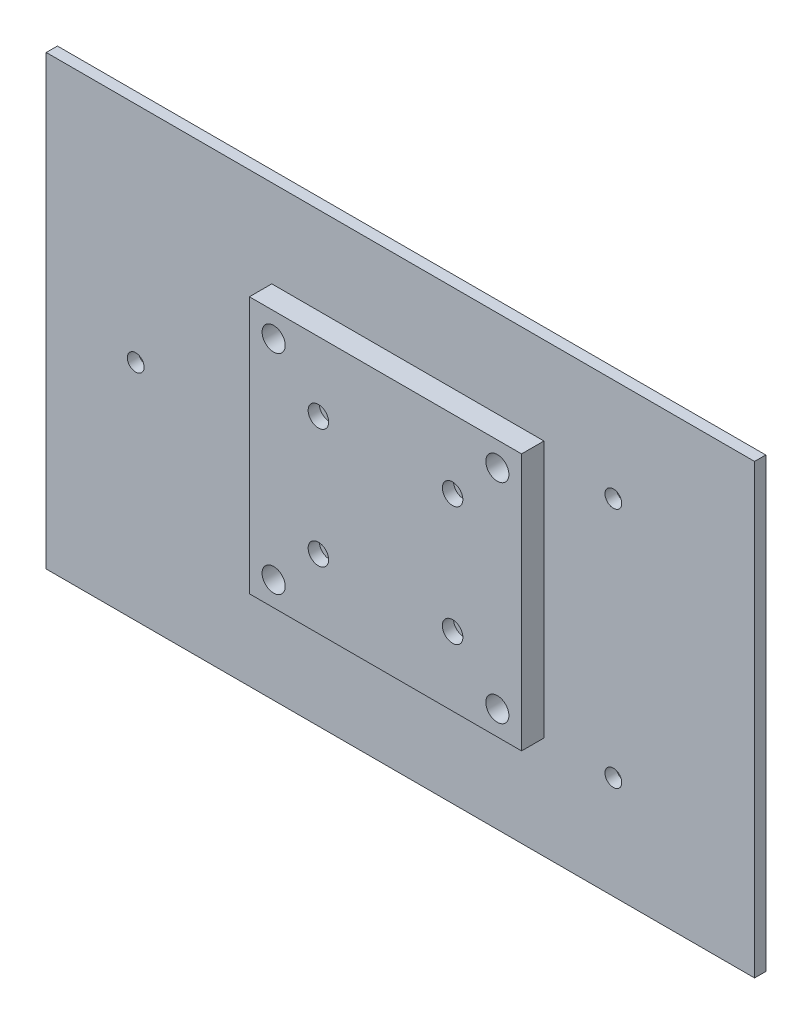
SolidWorks part; units mm, degrees
ref_plane "Alzado" through (0, 0, 0) normal (0, 0, 1) x (1, 0, 0)
ref_plane "Planta" through (0, 0, 0) normal (0, 1, 0) x (1, 0, 0)
ref_plane "Vista lateral" through (0, 0, 0) normal (1, 0, 0) x (0, 0, -1)
sketch "Croquis1" plane through (0, 0, 0) normal (0, 0, 1) x (1, 0, 0)
  line L1 (0, 0) -> (73, 0)
  line L2 (0, 0) -> (0, 69)
  line L3 (0, 69) -> (73, 69)
  line L4 (73, 0) -> (73, 69)
  circle A0 centre (6.5, 6.5) radius 3.1
  circle A1 centre (66.5, 6.5) radius 3.1
  circle A2 centre (66.5, 62.5) radius 3.1
  circle A3 centre (6.5, 62.5) radius 3.1
  circle A4 centre (18.5, 50.5) radius 1.25
  circle A5 centre (54.5, 50.5) radius 1.25
  circle A6 centre (54.5, 18.5) radius 1.25
  circle A7 centre (18.5, 18.5) radius 1.25
  dimension "D3" = 6.5
  dimension "D4" = 6.5
  dimension "D5" = 6.5
  dimension "D6" = 6.5
  dimension "D7" = 6.2
  dimension "D8" = 2.5
  dimension "D9" = 2.5
  dimension "D10" = 2.5
  dimension "D11" = 2.5
  dimension "D13" = 18.5
  dimension "D14" = 36
  dimension "D15" = 32
  dimension "D16" = 32
  dimension "D17" = 36
  dimension "D18" = 60
  dimension "D19" = 56
  dimension "D1" = 69
  dimension "D2" = 73
  dimension "D12" = 18.5
extrude "Saliente-Extruir1" add sketch "Croquis1" along normal blind 6
sketch "Croquis3" plane through (0, 0, 0) normal (0, 0, -1) x (-1, 0, 0)
  line L0 (60.5, -27.5) -> (60.5, 92.5)
  line L1 (60.5, 92.5) -> (-129.5, 92.5)
  line L2 (-129.5, 92.5) -> (-129.5, -27.5)
  line L3 (60.5, -27.5) -> (-129.5, -27.5)
  circle A0 centre (36.5, 32.5) radius 2.25
  circle A1 centre (-91.6232, 0.0693) radius 2.25
  circle A2 centre (-91.6232, 64.9307) radius 2.25
  circle A7 centre (-66.5, 62.5) radius 5
  circle A8 centre (-6.5, 62.5) radius 5
  circle A9 centre (-6.5, 6.5) radius 5
  circle A10 centre (-66.5, 6.5) radius 5
  circle A11 centre (-54.5, 50.5) radius 1.25
  circle A12 centre (-18.5, 50.5) radius 1.25
  circle A13 centre (-18.5, 18.5) radius 1.25
  circle A14 centre (-54.5, 18.5) radius 1.25
  dimension "D8" = 4.5
  dimension "D9" = 10
  dimension "D10" = 10
  dimension "D13" = 56
  dimension "D14" = 60
  dimension "D15" = 4.5
  dimension "D16" = 4.5
  dimension "D11" = 10
  dimension "D12" = 10
  dimension "D18" = 30
  dimension "D19" = 67
  dimension "D1" = 24
  dimension "D2" = 60
  dimension "D3" = 27.5693
  dimension "D4" = 37.8768
  dimension "D5" = 37.8768
  dimension "D6" = 120
  dimension "D7" = 190
  dimension "D17" = 27.5693
  dimension "D20" = 120
  dimension "D21" = 190
extrude "Saliente-Extruir2" add sketch "Croquis3" along normal blind 3
sketch "Croquis5" plane through (0, 0, 6) normal (0, 0, 1) x (1, 0, 0)
  circle A0 centre (18.5, 50.5) radius 2.75
  circle A1 centre (54.5, 50.5) radius 2.75
  circle A2 centre (54.5, 18.5) radius 2.75
  circle A3 centre (18.5, 18.5) radius 2.75
extrude "Cortar-Extruir1" cut sketch "Croquis5" against normal blind 3
